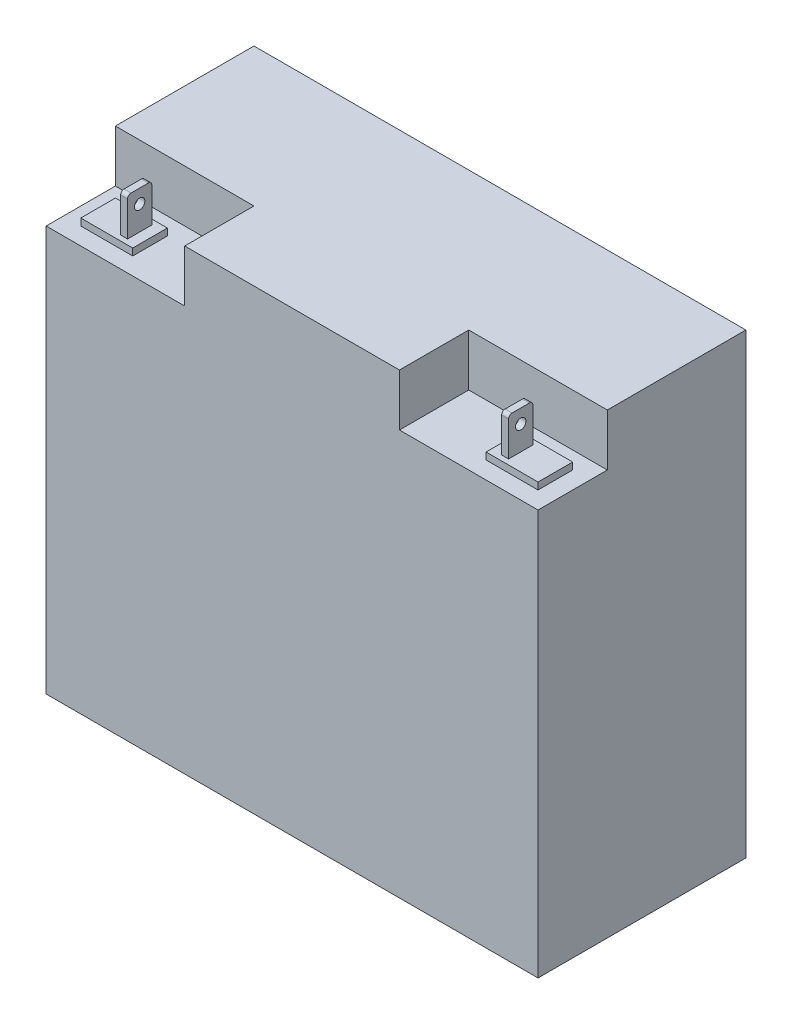
SolidWorks part; units mm, degrees
ref_plane "Front Plane" through (0, 0, 0) normal (0, 0, 1) x (1, 0, 0)
ref_plane "Top Plane" through (0, 0, 0) normal (0, 1, 0) x (1, 0, 0)
ref_plane "Right Plane" through (0, 0, 0) normal (1, 0, 0) x (0, 0, -1)
sketch "Sketch1" plane through (0, 0, 0) normal (0, 0, 1) x (1, 0, 0)
  line L1 (0, 0) -> (180.34, 0)
  line L2 (0, 0) -> (0, 167.64)
  line L3 (0, 167.64) -> (180.34, 167.64)
  line L4 (180.34, 0) -> (180.34, 167.64)
  dimension "D1" = 180.34
  dimension "D2" = 167.64
extrude "case" add sketch "Sketch1" along normal mid plane 76.2
sketch "Sketch2" plane through (0, 167.64, 0) normal (0, 1, 0) x (1, 0, 0)
  line L0 (90.17, 38.1) -> (90.17, -38.1) construction
  line L1 (0, -38.1) -> (50.8, -38.1)
  line L2 (0, -38.1) -> (0, -12.7)
  line L3 (0, -12.7) -> (50.8, -12.7)
  line L4 (180.34, 38.1) -> (0, 38.1)
  line L5 (0, 38.1) -> (0, -38.1)
  line L6 (0, -38.1) -> (180.34, -38.1)
  line L7 (180.34, -38.1) -> (180.34, 38.1)
  line L8 (180.34, 38.1) -> (0, 38.1)
  line L9 (0, 38.1) -> (0, -38.1)
  line L10 (0, -38.1) -> (180.34, -38.1)
  line L11 (180.34, -38.1) -> (180.34, 38.1)
  line L12 (50.8, -38.1) -> (50.8, -12.7)
  line L13 (180.34, -38.1) -> (129.54, -38.1)
  line L14 (180.34, -38.1) -> (180.34, -12.7)
  line L15 (180.34, -12.7) -> (129.54, -12.7)
  line L16 (129.54, -38.1) -> (129.54, -12.7)
  line M11 (0, 38.1) -> (0, -38.1)
  line M12 (0, -38.1) -> (180.34, -38.1)
  line M13 (180.34, -38.1) -> (180.34, 38.1)
  dimension "D2" = 50.8
  dimension "D3" = 25.4
  dimension "D1" = 0
extrude "top hole" cut sketch "Sketch2" against normal blind 19.05 contours L12 L3 M12 M11 | L16 L10 L15 M13
sketch "Sketch3" plane through (0, 148.59, 0) normal (0, 1, 0) x (1, 0, 0)
  line L1 (6.35, -31.75) -> (25.4, -31.75)
  line L2 (6.35, -31.75) -> (6.35, -19.05)
  line L3 (6.35, -19.05) -> (25.4, -19.05)
  line L4 (0, -38.1) -> (50.8, -38.1)
  line L5 (50.8, -38.1) -> (50.8, -12.7)
  line L6 (50.8, -12.7) -> (0, -12.7)
  line L7 (0, -12.7) -> (0, -38.1)
  line L8 (0, -38.1) -> (50.8, -38.1)
  line L9 (50.8, -38.1) -> (50.8, -12.7)
  line L10 (50.8, -12.7) -> (0, -12.7)
  line L11 (0, -12.7) -> (0, -38.1)
  line L12 (25.4, -31.75) -> (25.4, -19.05)
  dimension "D2" = 19.05
  dimension "D3" = 6.35
  dimension "D4" = 6.35
  dimension "D5" = 12.7
  dimension "D1" = 0
extrude "Boss-Extrude2" add sketch "Sketch3" along normal blind 2.54 contours L1 L12 L3 L2
sketch "Sketch4" plane through (0, 151.13, 0) normal (0, 1, 0) x (1, 0, 0)
  line L0 (21.59, -25.4) -> (25.4, -25.4) construction
  line L1 (19.05, -20.955) -> (21.59, -20.955)
  line L2 (19.05, -20.955) -> (19.05, -29.845)
  line L3 (19.05, -29.845) -> (21.59, -29.845)
  line L4 (21.59, -20.955) -> (21.59, -29.845)
  line L5 (25.4, -31.75) -> (25.4, -19.05) construction
  dimension "D1" = 8.89
  dimension "D2" = 2.54
  dimension "D3" = 3.81
extrude "Boss-Extrude3" add sketch "Sketch4" along normal offset from surface (13.97 mm away) 2.54 up to face at (90.17, 167.64, 6.35)
sketch "Sketch5" plane through (21.59, 0, 0) normal (1, 0, 0) x (0, 0, -1)
  line L0 (-25.4, 165.1) -> (-25.4, 160.02) construction
  line L4 (-20.955, 151.13) -> (-20.955, 165.1)
  line L5 (-20.955, 165.1) -> (-29.845, 165.1)
  line L6 (-29.845, 165.1) -> (-29.845, 151.13)
  line L7 (-29.845, 151.13) -> (-20.955, 151.13)
  line L8 (-20.955, 151.13) -> (-20.955, 163.83)
  line L9 (-22.225, 165.1) -> (-28.575, 165.1)
  line L10 (-29.845, 163.83) -> (-29.845, 151.13)
  line L11 (-29.845, 151.13) -> (-20.955, 151.13)
  circle A0 centre (-25.4, 160.02) radius 1.905
  arc A1 (-20.955, 163.83) -> (-22.225, 165.1) centre (-22.225, 163.83) ccw
  arc A2 (-28.575, 165.1) -> (-29.845, 163.83) centre (-28.575, 163.83) ccw
  dimension "D2" = 1.27
  dimension "D3" = 3.81
  dimension "D4" = 5.08
  dimension "D1" = 0
extrude "Cut-Extrude2" cut sketch "Sketch5" against normal up to next (2.54 mm away)
ref_plane "Plane1" through (90.17, 0, 0) normal (1, 0, 0) x (0, 0, -1)
sketch "Sketch6" plane through (0, 148.59, 0) normal (0, 1, 0) x (1, 0, 0)
  line L0 (90.17, -38.1) -> (90.17, 38.1) construction
  line L1 (173.99, -19.05) -> (173.99, -31.75)
  line L2 (154.94, -19.05) -> (173.99, -19.05)
  line L3 (154.94, -31.75) -> (154.94, -19.05)
  line L4 (6.35, -31.75) -> (25.4, -31.75)
  line L5 (25.4, -31.75) -> (25.4, -19.05)
  line L6 (25.4, -19.05) -> (6.35, -19.05)
  line L7 (6.35, -19.05) -> (6.35, -31.75)
  line L8 (129.54, -38.1) -> (129.54, -12.7)
  line L9 (129.54, -12.7) -> (180.34, -12.7)
  line L10 (180.34, -12.7) -> (180.34, 38.1)
  line L11 (180.34, 38.1) -> (0, 38.1)
  line L12 (0, 38.1) -> (0, -12.7)
  line L13 (0, -12.7) -> (50.8, -12.7)
  line L14 (50.8, -12.7) -> (50.8, -38.1)
  line L15 (50.8, -38.1) -> (129.54, -38.1)
  line L16 (129.54, -38.1) -> (129.54, -12.7)
  line L17 (129.54, -12.7) -> (180.34, -12.7)
  line L18 (180.34, -12.7) -> (180.34, 38.1)
  line L19 (180.34, 38.1) -> (0, 38.1)
  line L20 (0, 38.1) -> (0, -12.7)
  line L21 (0, -12.7) -> (50.8, -12.7)
  line L22 (50.8, -12.7) -> (50.8, -38.1)
  line L23 (50.8, -38.1) -> (129.54, -38.1)
  line L24 (6.35, -31.75) -> (25.4, -31.75)
  line L25 (25.4, -31.75) -> (25.4, -19.05)
  line L26 (25.4, -19.05) -> (6.35, -19.05)
  line L27 (6.35, -19.05) -> (6.35, -31.75)
  line L28 (173.99, -31.75) -> (154.94, -31.75)
  dimension "D1" = 0
  dimension "D2" = 0
extrude "Boss-Extrude4" add sketch "Sketch6" along normal up to surface (2.54 mm away) contours L28 L1 L2 L3 up to face at (15.875, 151.13, 25.4)
mirror "Mirror1" about plane through (90.17, 0, 0) normal (1, 0, 0) of "Cut-Extrude2", "Boss-Extrude3"
